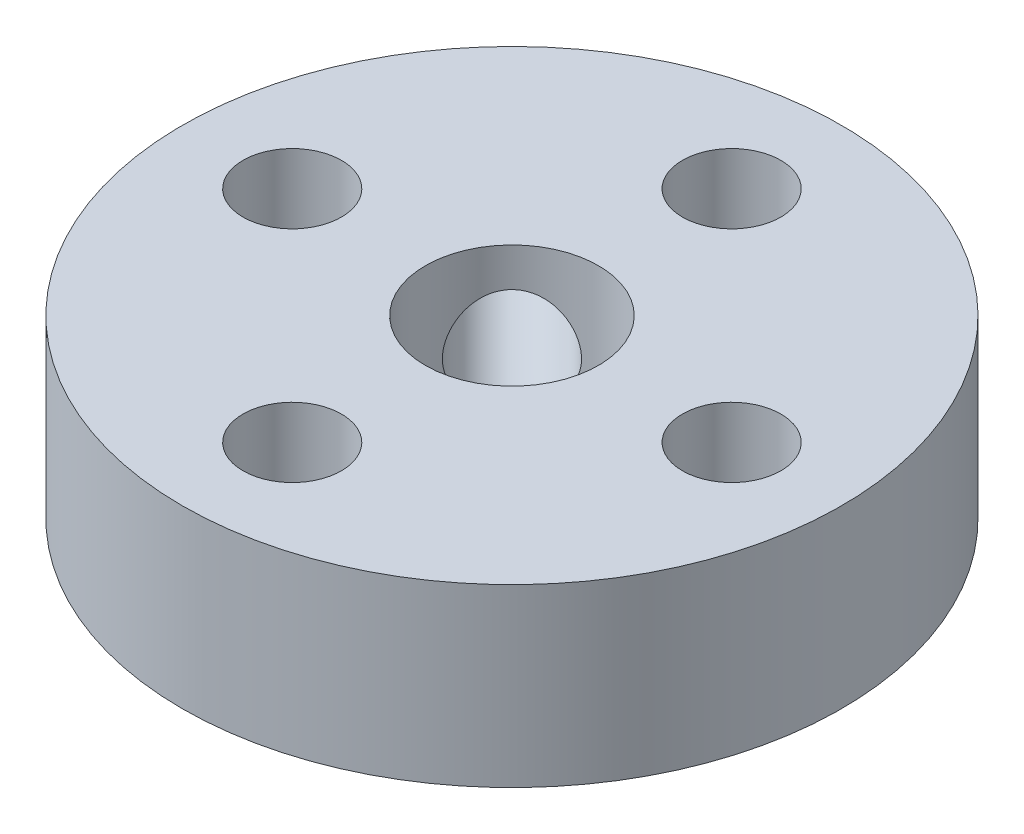
SolidWorks part; units mm, degrees
ref_plane "Front Plane" through (0, 0, 0) normal (0, 0, 1) x (1, 0, 0)
ref_plane "Top Plane" through (0, 0, 0) normal (0, 1, 0) x (1, 0, 0)
ref_plane "Right Plane" through (0, 0, 0) normal (1, 0, 0) x (0, 0, -1)
sketch "Sketch2" plane through (0, 0, 0) normal (0, 1, 0) x (1, 0, 0)
  line L0 (0, 6.35) -> (0, 0) construction
  circle A0 centre (0, 0) radius 9.525
  circle A1 centre (0, 6.35) radius 1.4224
  circle A2 centre (6.35, 0) radius 1.4224
  circle A3 centre (0, -6.35) radius 1.4224
  circle A4 centre (-6.35, 0) radius 1.4224
  circle A5 centre (0, 0) radius 2.5
  point P14 (0, 0)
  dimension "D1" = 2.8448
  dimension "D2" = 19.05
  dimension "D5" = 5
  dimension "D3" = 6.35
  dimension "D4" = 4
extrude "Boss-Extrude1" add sketch "Sketch2" along normal blind 5.08
sketch "Sketch4" plane through (0, 0, 0) normal (0, 0, 1) x (1, 0, 0)
  line L0 (0, 0) -> (0, 9.1437) construction
ref_plane "Plane1" through (0, 0, 0) normal (0.7071, 0, 0.7071) x (0.7071, 0, -0.7071)
sketch "Sketch7" plane through (0, 0, 0) normal (0.7071, 0, 0.7071) x (0.7071, 0, -0.7071)
  line L0 (-9.525, 5.08) -> (9.525, 0) construction
  circle A0 centre (0, 2.54) radius 1.4224
  dimension "D1" = 2.8448
extrude "Cut-Extrude1" cut sketch "Sketch7" against normal up to next
